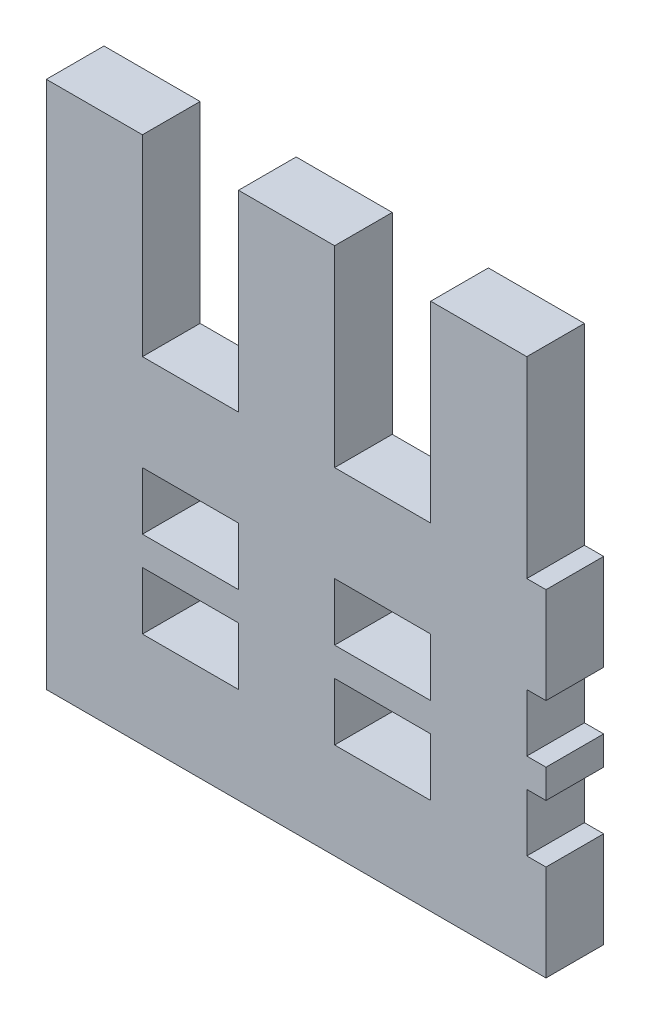
SolidWorks part; units mm, degrees
ref_plane "Plan de face" through (0, 0, 0) normal (0, 0, 1) x (1, 0, 0)
ref_plane "Plan de dessus" through (0, 0, 0) normal (0, 1, 0) x (1, 0, 0)
ref_plane "Plan de droite" through (0, 0, 0) normal (1, 0, 0) x (0, 0, -1)
sketch "Esquisse1" plane through (0, 0, 0) normal (0, 0, 1) x (1, 0, 0)
  line L0 (-35.4148, 38.6386) -> (-35.4148, 48.6386)
  line L1 (-50.4148, 33.6386) -> (-24.4148, 33.6386)
  line L2 (-50.4148, 33.6386) -> (-50.4148, 38.6386)
  line L3 (-50.4148, 38.6386) -> (-24.4148, 38.6386)
  line L4 (-24.4148, 33.6386) -> (-24.4148, 38.6386)
  line L5 (-50.4148, 38.6386) -> (-45.4148, 38.6386)
  line L6 (-50.4148, 38.6386) -> (-50.4148, 48.6386)
  line L7 (-50.4148, 48.6386) -> (-45.4148, 48.6386)
  line L8 (-45.4148, 38.6386) -> (-45.4148, 48.6386)
  line L9 (-40.4148, 48.6386) -> (-35.4148, 48.6386)
  line L10 (-40.4148, 38.6386) -> (-40.4148, 48.6386)
  line L11 (-25.4148, 38.6386) -> (-25.4148, 48.6386)
  line L12 (-30.4148, 48.6386) -> (-25.4148, 48.6386)
  line L13 (-30.4148, 38.6386) -> (-30.4148, 48.6386)
  line L15 (-50.4148, 33.6386) -> (-45.4148, 33.6386)
  line L16 (-50.4148, 33.6386) -> (-50.4148, 30.6386)
  line L17 (-50.4148, 30.6386) -> (-45.4148, 30.6386)
  line L18 (-45.4148, 33.6386) -> (-45.4148, 30.6386)
  line L19 (-40.4148, 33.6386) -> (-35.4148, 33.6386)
  line L20 (-40.4148, 33.6386) -> (-40.4148, 30.6386)
  line L21 (-40.4148, 30.6386) -> (-35.4148, 30.6386)
  line L22 (-35.4148, 33.6386) -> (-35.4148, 30.6386)
  line L23 (-30.4148, 33.6386) -> (-25.4148, 33.6386)
  line L24 (-30.4148, 33.6386) -> (-30.4148, 30.6386)
  line L25 (-30.4148, 30.6386) -> (-25.4148, 30.6386)
  line L26 (-25.4148, 33.6386) -> (-25.4148, 30.6386)
  line L27 (-24.4148, 30.6386) -> (-50.4148, 30.6386)
  line L28 (-24.4148, 30.6386) -> (-24.4148, 29.1386)
  line L29 (-24.4148, 29.1386) -> (-50.4148, 29.1386)
  line L30 (-50.4148, 30.6386) -> (-50.4148, 29.1386)
  line L31 (-25.4148, 29.1386) -> (-30.4148, 29.1386)
  line L32 (-25.4148, 29.1386) -> (-25.4148, 26.1386)
  line L33 (-25.4148, 26.1386) -> (-30.4148, 26.1386)
  line L34 (-30.4148, 29.1386) -> (-30.4148, 26.1386)
  line L35 (-35.4148, 29.1386) -> (-40.4148, 29.1386)
  line L36 (-35.4148, 29.1386) -> (-35.4148, 26.1386)
  line L37 (-35.4148, 26.1386) -> (-40.4148, 26.1386)
  line L38 (-40.4148, 29.1386) -> (-40.4148, 26.1386)
  line L39 (-45.4148, 29.1386) -> (-50.4148, 29.1386)
  line L40 (-45.4148, 29.1386) -> (-45.4148, 26.1386)
  line L41 (-45.4148, 26.1386) -> (-50.4148, 26.1386)
  line L42 (-50.4148, 29.1386) -> (-50.4148, 26.1386)
  line L43 (-24.4148, 26.1386) -> (-50.4148, 26.1386)
  line L44 (-24.4148, 26.1386) -> (-24.4148, 21.1386)
  line L45 (-24.4148, 21.1386) -> (-50.4148, 21.1386)
  line L46 (-50.4148, 26.1386) -> (-50.4148, 21.1386)
  dimension "D1" = 10
  dimension "D2" = 5
  dimension "D3" = 26
  dimension "D4" = 5
  dimension "D6" = 3
  dimension "D7" = 3
  dimension "D8" = 3
  dimension "D9" = 1.5
  dimension "D10" = 3
  dimension "D11" = 3
  dimension "D12" = 3
  dimension "D13" = 5
  dimension "D5" = 3
extrude "Boss.-Extru.1" add sketch "Esquisse1" along normal blind 3 contours L41 L46 L45 L44 L43 L33 L37 | L3 L8 L7 L6 | L10 L3 L0 L9 | L13 L3 L11 L12 | L1 L4 L3 L2 | L26 L1 L24 L25 | L22 L1 L20 L21 | L18 L1 L16 L17 | L17 L30 L29 L28 L27 L25 L21 | L29 L42 L41 L40 | L29 L38 L37 L36 | L29 L34 L33 L32
